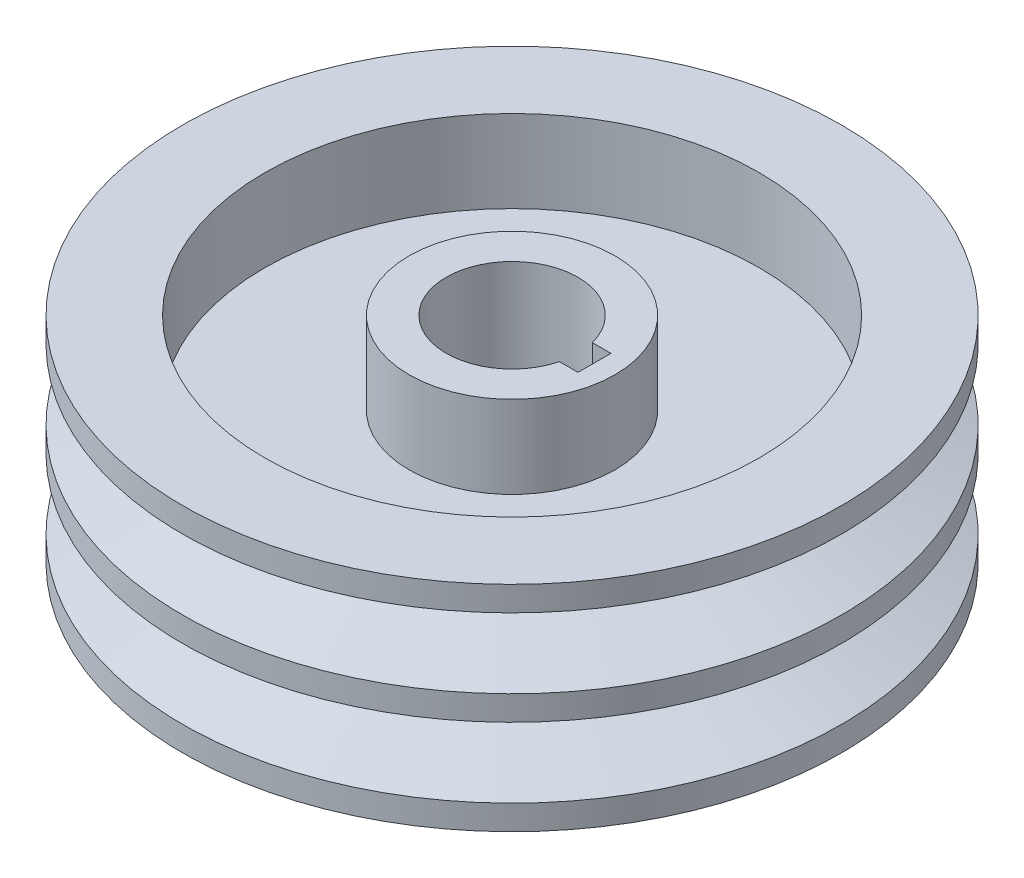
SolidWorks part; units mm, degrees
ref_plane "前基準面" through (0, 0, 0) normal (0, 0, 1) x (1, 0, 0)
ref_plane "上基準面" through (0, 0, 0) normal (0, 1, 0) x (1, 0, 0)
ref_plane "右基準面" through (0, 0, 0) normal (1, 0, 0) x (0, 0, -1)
sketch "草圖1" plane through (0, 0, 0) normal (0, 0, 1) x (1, 0, 0)
  line L7 (0, 0) -> (0, 59.7247) construction
  line L8 (30, -13) -> (30, -3)
  line L14 (30, 0) -> (0, 0) construction
  line L15 (30, 13) -> (40, 13)
  line L16 (40, 13) -> (40, 10)
  line L20 (40, -1.5) -> (40, 1.5)
  line L24 (40, -13) -> (40, -10)
  line L25 (30, -13) -> (40, -13)
  line L26 (27.3872, 5.75) -> (40.7186, 5.75) construction
  line L27 (40, 10) -> (32, 7.0882)
  line L28 (32, 7.0882) -> (32, 4.4118)
  line L29 (32, 4.4118) -> (40, 1.5)
  line L30 (32, -4.4118) -> (40, -1.5)
  line L31 (32, -7.0882) -> (32, -4.4118)
  line L32 (40, -10) -> (32, -7.0882)
  line L33 (30, 3) -> (12.5, 3)
  line L34 (12.5, 3) -> (12.5, 13)
  line L35 (12.5, 13) -> (8, 13)
  line L36 (8, 13) -> (8, -13)
  line L37 (12.5, -13) -> (8, -13)
  line L38 (12.5, -3) -> (12.5, -13)
  line L39 (30, -3) -> (12.5, -3)
  line L40 (30, 3) -> (30, 13)
  point P12 (40, 0)
  dimension "D1" = 8
  dimension "D2" = 40
  dimension "D3" = 26
  dimension "D4" = 3
  dimension "D5" = 3
  dimension "D6" = 30
  dimension "D7" = 40
  dimension "D8" = 6
  dimension "D9" = 8
  dimension "D10" = 12.5
revolve "旋轉1" add sketch "草圖1" angle 360 about L7
sketch "草圖2" plane through (0, 13, 0) normal (0, 1, 0) x (1, 0, 0)
  line L0 (30, 0) -> (0, 0) construction
  line L1 (0, -2) -> (10, -2)
  line L2 (0, -2) -> (0, 2)
  line L3 (0, 2) -> (10, 2)
  line L4 (10, -2) -> (10, 2)
  line L5 (0, -2) -> (10, 2) construction
  line L6 (0, 2) -> (10, -2) construction
  line L7 (0, 0) -> (-8, 0) construction
  circle A0 centre (0, 0) radius 8 construction
  point P0 (5, 0)
  dimension "D2" = 18
  dimension "D1" = 4
extrude "除料-伸長1" cut sketch "草圖2" against normal through all
